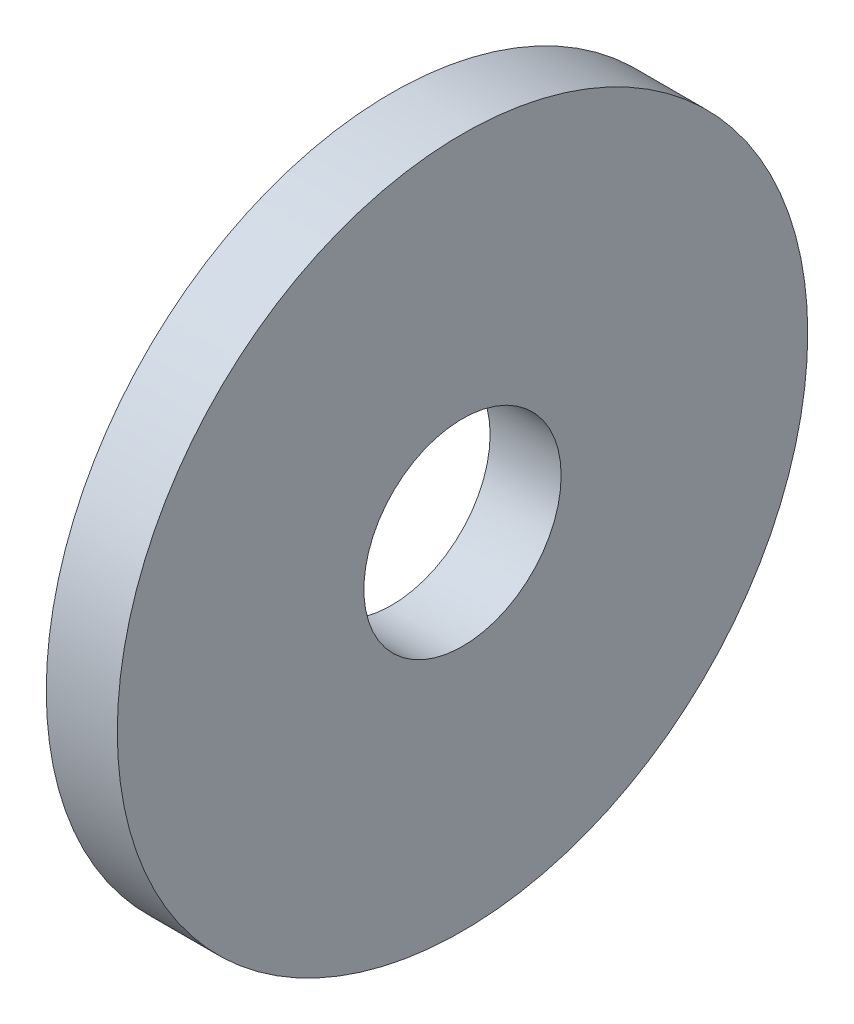
SolidWorks part; units mm, degrees
ref_plane "Front Plane" through (0, 0, 0) normal (0, 0, 1) x (1, 0, 0)
ref_plane "Top Plane" through (0, 0, 0) normal (0, 1, 0) x (1, 0, 0)
ref_plane "Right Plane" through (0, 0, 0) normal (1, 0, 0) x (0, 0, -1)
sketch "Sketch1" plane through (0, 0, 0) normal (1, 0, 0) x (0, 0, -1)
  circle A0 centre (0, 0) radius 5.5562
  circle A1 centre (0, 0) radius 1.5875
  dimension "OD" = 11.1125
  dimension "ID" = 3.175
extrude "Boss-Extrude1" add sketch "Sketch1" along normal blind 1.143
